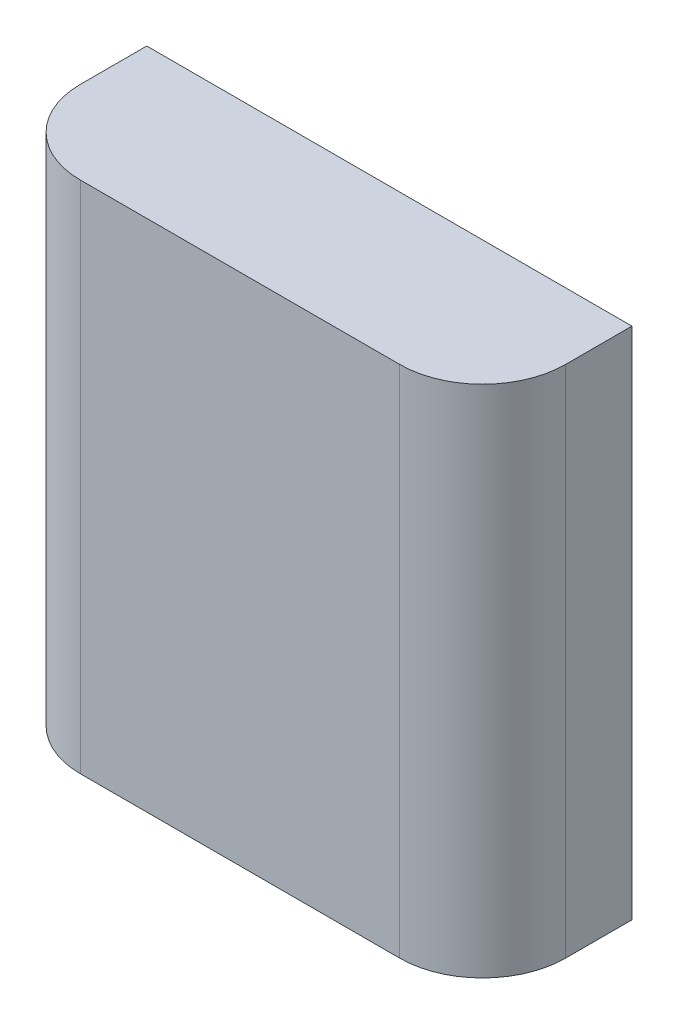
SolidWorks part; units mm, degrees
ref_plane "Front" through (0, 0, 0) normal (0, 0, 1) x (1, 0, 0)
ref_plane "Top" through (0, 0, 0) normal (0, 1, 0) x (1, 0, 0)
ref_plane "Right" through (0, 0, 0) normal (1, 0, 0) x (0, 0, -1)
sketch "Sketch1" plane through (0, 0, 0) normal (0, 0, 1) x (1, 0, 0)
  line L1 (-29.25, -31) -> (29.25, -31)
  line L2 (-29.25, -31) -> (-29.25, 31)
  line L3 (-29.25, 31) -> (29.25, 31)
  line L4 (29.25, -31) -> (29.25, 31)
  line L5 (-29.25, -31) -> (29.25, 31) construction
  line L6 (-29.25, 31) -> (29.25, -31) construction
  point P0 (0, 0)
  dimension "D1" = 58.5
  dimension "D2" = 62
extrude "Boss-Extrude1" add sketch "Sketch1" along normal blind 18
fillet "Fillet1" radius 10 2 edges at (-29.25, 0, 18) (29.25, 0, 18)
